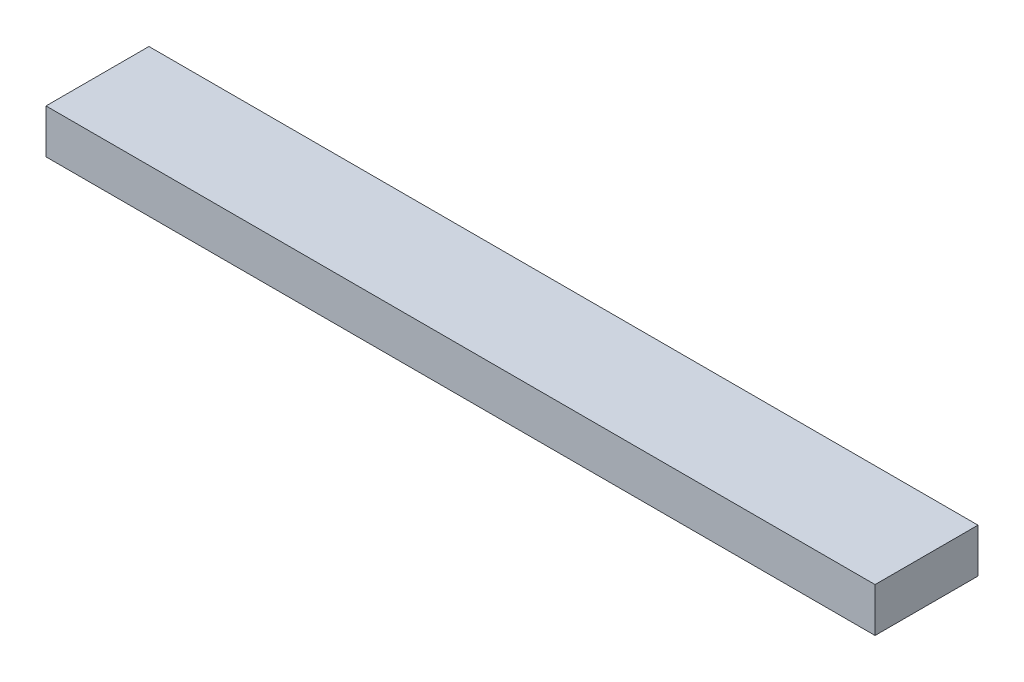
SolidWorks part; units mm, degrees
material "Pine"
ref_plane "Front Plane" through (0, 0, 0) normal (0, 0, 1) x (1, 0, 0)
ref_plane "Top Plane" through (0, 0, 0) normal (0, 1, 0) x (1, 0, 0)
ref_plane "Right Plane" through (0, 0, 0) normal (1, 0, 0) x (0, 0, -1)
sketch "Sketch1" plane through (0, 0, 0) normal (0, 1, 0) x (1, 0, 0)
  line L1 (0, 0) -> (715.9625, 0)
  line L2 (0, 0) -> (0, 88.9)
  line L3 (0, 88.9) -> (715.9625, 88.9)
  line L4 (715.9625, 0) -> (715.9625, 88.9)
  dimension "D1" = 88.9
  dimension "D2" = 715.9625
extrude "Boss-Extrude1" add sketch "Sketch1" along normal blind 38.1
